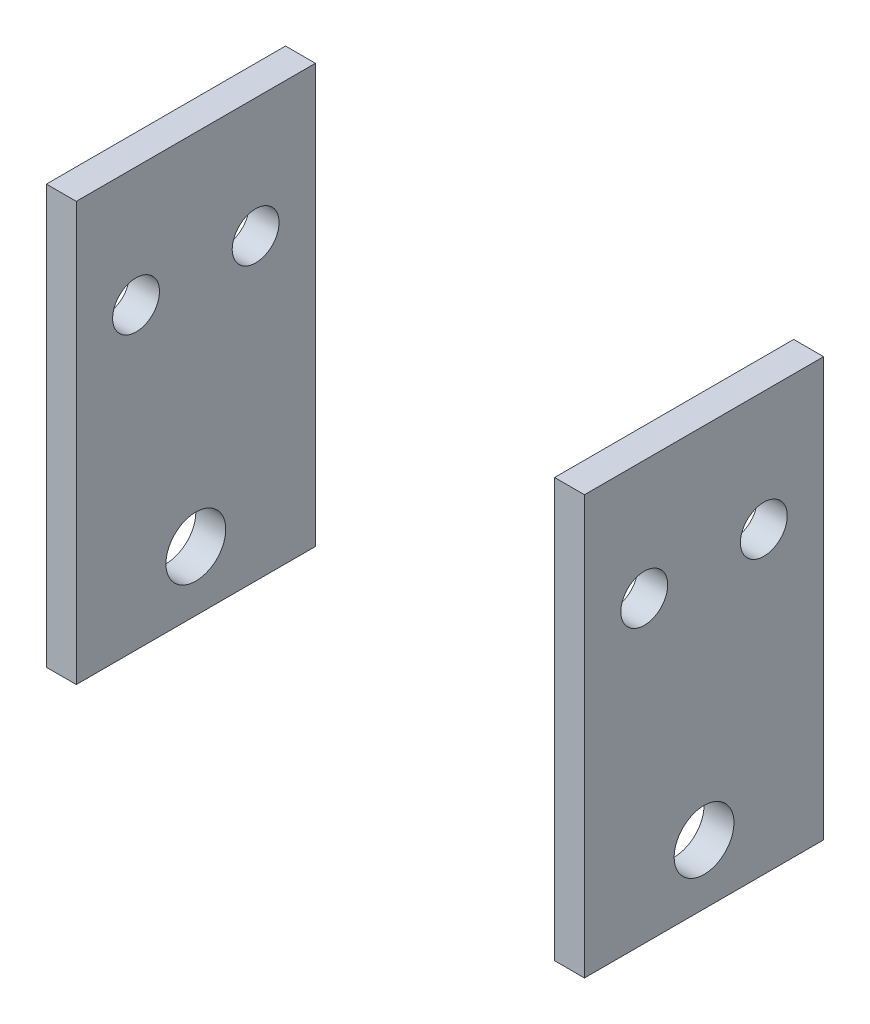
SolidWorks part; units mm, degrees
ref_plane "Front Plane" through (0, 0, 0) normal (0, 0, 1) x (1, 0, 0)
ref_plane "Top Plane" through (0, 0, 0) normal (0, 1, 0) x (1, 0, 0)
ref_plane "Right Plane" through (0, 0, 0) normal (1, 0, 0) x (0, 0, -1)
sketch "Sketch1" plane through (0, 0, 0) normal (0, 0, 1) x (1, 0, 0)
  line L1 (69.85, 57.15) -> (73.025, 57.15)
  line L2 (69.85, 57.15) -> (69.85, -11.5131)
  line L3 (69.85, -11.5131) -> (73.025, -11.5131)
  line L4 (73.025, 57.15) -> (73.025, -11.5131)
  line L6 (44.45, 19.05) -> (44.45, 46.5616) construction
  line L7 (15.875, 57.15) -> (15.875, -11.5131)
  line L8 (19.05, -11.5131) -> (15.875, -11.5131)
  line L9 (19.05, 57.15) -> (19.05, -11.5131)
  line L10 (19.05, 57.15) -> (15.875, 57.15)
  dimension "D2" = 3.175
  dimension "D3" = 25.4
  dimension "D4" = 25.4
extrude "Boss-Extrude1" add sketch "Sketch1" along normal blind 25.4
sketch "Sketch2" plane through (73.025, 0, 0) normal (1, 0, 0) x (0, 0, -1)
  line L0 (-25.4, -11.5131) -> (-25.4, 57.15) construction
  line L2 (-50.8, 17.0619) -> (-25.4, 17.0619) construction
  line L3 (0, -11.5131) -> (0, 57.15) construction
  circle A0 centre (-12.7, 4.3619) radius 3.175
  circle A1 centre (-44.45, 4.3619) radius 3.175 construction
  circle A2 centre (-19.05, 29.7619) radius 2.4892
  circle A3 centre (-6.35, 29.7619) radius 2.4892
  dimension "D1" = 12.7
  dimension "D2" = 4.9784
  dimension "D3" = 12.7
  dimension "D4" = 6.35
  dimension "D5" = 6.35
extrude "Cut-Extrude1" cut sketch "Sketch2" against normal through all
sketch "Sketch3" plane through (73.025, 0, 0) normal (1, 0, 0) x (0, 0, -1)
  line L0 (0, -11.5131) -> (0, 57.15) construction
  line L1 (0, -1.9881) -> (-25.4, -1.9881)
  line L2 (0, -1.9881) -> (0, -11.5131)
  line L3 (0, -11.5131) -> (-25.4, -11.5131)
  line L4 (-25.4, -1.9881) -> (-25.4, -11.5131)
  line L6 (0, 42.4619) -> (-25.4, 42.4619)
  line L7 (0, 42.4619) -> (0, 57.15)
  line L8 (0, 57.15) -> (-25.4, 57.15)
  line L9 (-25.4, 42.4619) -> (-25.4, 57.15)
  circle A0 centre (-19.05, 29.7619) radius 2.4892 construction
  circle A1 centre (-12.7, 4.3619) radius 3.175 construction
  dimension "D2" = 6.35
  dimension "D1" = 12.7
extrude "Cut-Extrude3" cut sketch "Sketch3" against normal through all
equation "\"Thick\"= \"in\""
